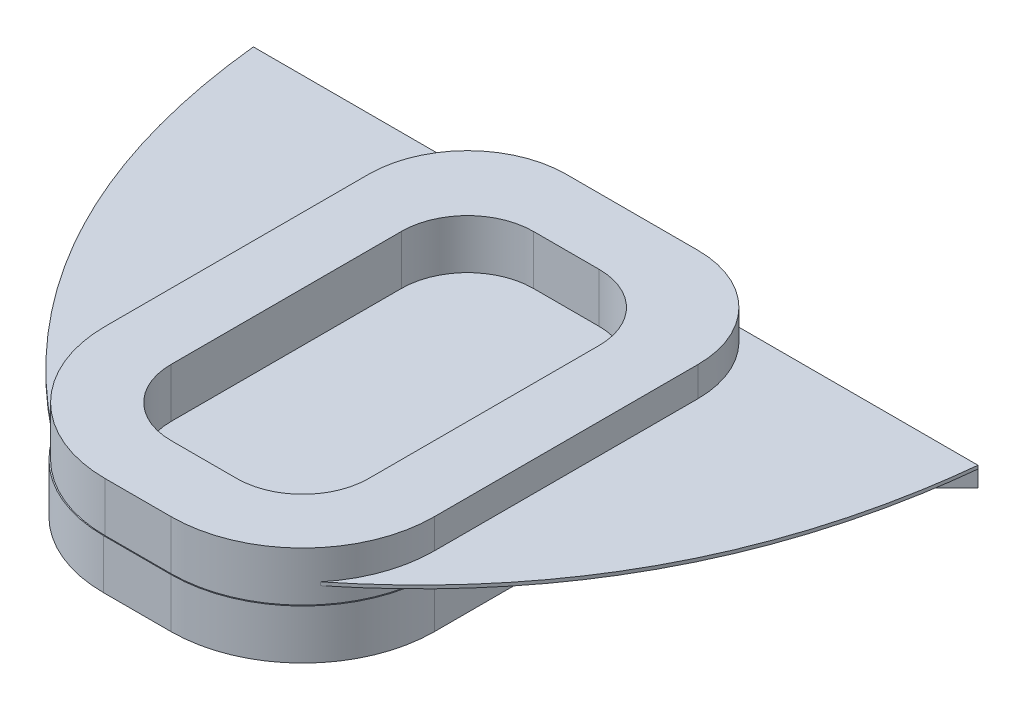
SolidWorks part; units mm, degrees
ref_plane "前视基准面" through (0, 0, 0) normal (0, 0, 1) x (1, 0, 0)
ref_plane "上视基准面" through (0, 0, 0) normal (0, 1, 0) x (1, 0, 0)
ref_plane "右视基准面" through (0, 0, 0) normal (1, 0, 0) x (0, 0, -1)
sketch "草图1" plane through (0, 0, 0) normal (0, 1, 0) x (1, 0, 0)
  line L1 (-4.05, 15.05) -> (4.05, 15.05)
  line L2 (-10.05, 9.05) -> (-10.05, -7.05)
  line L3 (-2.05, -15.05) -> (2.05, -15.05)
  line L4 (10.05, 9.05) -> (10.05, -7.05)
  line L5 (-10.05, 15.05) -> (10.05, -15.05) construction
  line L6 (-10.05, -15.05) -> (10.05, 15.05) construction
  arc A0 (-4.05, 15.05) -> (-10.05, 9.05) centre (-4.05, 9.05) ccw
  arc A1 (4.05, 15.05) -> (10.05, 9.05) centre (4.05, 9.05) cw
  arc A2 (2.05, -15.05) -> (10.05, -7.05) centre (2.05, -7.05) ccw
  arc A3 (-10.05, -7.05) -> (-2.05, -15.05) centre (-2.05, -7.05) ccw
  point P0 (0, 0)
  dimension "D3" = 6
  dimension "D4" = 8
  dimension "D1" = 20.1
  dimension "D2" = 30.1
extrude "凸台-拉伸1" add sketch "草图1" along normal blind 3
sketch "草图2" plane through (0, 3, 0) normal (0, 1, 0) x (1, 0, 0)
  line L0 (-7, -10) -> (-7, -13)
  line L1 (-2, 12) -> (-20, 12)
  line L2 (-2, 12) -> (-2, 14)
  line L3 (-2, 14) -> (-20, 14)
  line L4 (-20, 12) -> (-20, 14)
  line L5 (-7, 12) -> (-9, 12)
  line L6 (-7, 12) -> (-7, -10)
  line L7 (-7, -10) -> (-9, -10)
  line L8 (-9, 12) -> (-9, -10)
  line L9 (-7, -13) -> (-9, -10)
  line L10 (-20, 14) -> (-22, 14)
  line L11 (-22, 14) -> (-20, 12)
  line L12 (0, 0) -> (0, 16.1646) construction
  line L13 (20, 14) -> (22, 14)
  line L14 (22, 14) -> (20, 12)
  line L15 (7, -10) -> (7, -13)
  line L16 (7, -13) -> (9, -10)
  line L17 (7, -10) -> (9, -10)
  line L18 (9, 12) -> (9, -10)
  line L19 (7, 12) -> (9, 12)
  line L20 (7, 12) -> (7, -10)
  line L21 (2, 14) -> (20, 14)
  line L22 (20, 12) -> (20, 14)
  line L23 (2, 12) -> (20, 12)
  line L24 (2, 12) -> (2, 14)
  point P4 (-7, -13)
  point P11 (-22, 14)
  arc M9 (-4.05, 15.05) -> (-10.05, 9.05) centre (-4.05, 9.05) ccw
  arc M15 (10.05, 9.05) -> (4.05, 15.05) centre (4.05, 9.05) ccw
  dimension "D1" = 2
  dimension "D2" = 18
  dimension "D3" = 2
  dimension "D4" = 22
extrude "凸台-拉伸2" add sketch "草图2" along normal blind 1 contours L1 L8 L7 L6 | L2 L3 L1 M9 | L4 L1 L3 M9 | L10 L11 L4 | L9 L0 L7 | L24 L23 L19 L21 M15 | L23 L22 L21 M15 | L22 L14 L13 | L19 L20 L17 L18 | L17 L15 L16
sketch "草图3" plane through (0, 4, 0) normal (0, 1, 0) x (1, 0, 0)
  line L0 (-7, -13) -> (-7, 14)
  line L1 (-2, 14) -> (-7.4408, 14) construction
  line L2 (0, 0) -> (0, 19.1475) construction
  line L3 (7, -13) -> (7, 14)
  line L4 (-22, 14) -> (-7, 14)
  line L5 (22, 14) -> (7, 14)
  spline S0 degree 2 poles (-22, 14) (-20.2033, -3.1492) (-7, -13) knots 0 0 0 1 1 1
  spline S1 degree 2 poles (22, 14) (20.2033, -3.1492) (7, -13) knots 0 0 0 1 1 1
extrude "凸台-拉伸3" add sketch "草图3" along normal blind 0.2
sketch "草图4" plane through (0, 3, 0) normal (0, 1, 0) x (1, 0, 0)
  line L1 (-4, 15) -> (4, 15)
  line L2 (-10, 9) -> (-10, -7)
  line L3 (-2, -15) -> (2, -15)
  line L4 (10, 9) -> (10, -7)
  line L5 (-10, 15) -> (10, -15) construction
  line L6 (-10, -15) -> (10, 15) construction
  line L7 (-2, 11) -> (2, 11)
  line L8 (-6, 7) -> (-6, -7)
  line L9 (-2, -11) -> (2, -11)
  line L10 (6, 7) -> (6, -7)
  line L11 (-6, 11) -> (6, -11) construction
  line L12 (-6, -11) -> (6, 11) construction
  arc A0 (-4, 15) -> (-10, 9) centre (-4, 9) ccw
  arc A1 (4, 15) -> (10, 9) centre (4, 9) cw
  arc A2 (2, -15) -> (10, -7) centre (2, -7) ccw
  arc A3 (-10, -7) -> (-2, -15) centre (-2, -7) ccw
  arc A4 (-2, 11) -> (-6, 7) centre (-2, 7) ccw
  arc A5 (2, 11) -> (6, 7) centre (2, 7) cw
  arc A6 (2, -11) -> (6, -7) centre (2, -7) ccw
  arc A7 (-6, -7) -> (-2, -11) centre (-2, -7) ccw
  point P0 (0, 0)
  point P18 (0, 0)
  dimension "D3" = 6
  dimension "D4" = 8
  dimension "D7" = 4
  dimension "D1" = 20
  dimension "D2" = 30
  dimension "D5" = 12
  dimension "D6" = 22
extrude "凸台-拉伸4" add sketch "草图4" along normal blind 3
scale "缩放比例1" scale about origin uniform scaling yes scale factor 0.1
